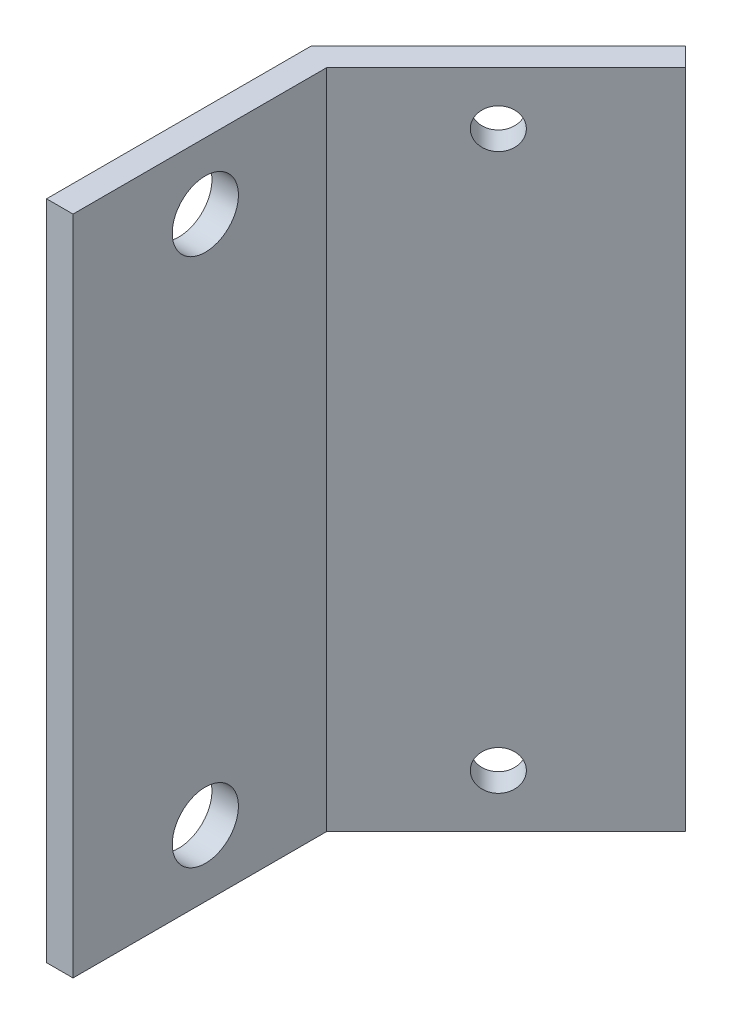
SolidWorks part; units mm, degrees
ref_plane "Plan de face" through (0, 0, 0) normal (0, 0, 1) x (1, 0, 0)
ref_plane "Plan de dessus" through (0, 0, 0) normal (0, 1, 0) x (1, 0, 0)
ref_plane "Plan de droite" through (0, 0, 0) normal (1, 0, 0) x (0, 0, -1)
sketch "Esquisse1" plane through (0, 0, 0) normal (0, 1, 0) x (1, 0, 0)
  line L0 (0, 0) -> (0, 20)
  line L1 (0, 20) -> (14.1421, 34.1421)
  line L2 (14.1421, 34.1421) -> (15.5563, 32.7279)
  line L3 (15.5563, 32.7279) -> (2, 19.1716)
  line L4 (2, 19.1716) -> (2, 0)
  line L5 (2, 0) -> (0, 0)
  dimension "D1" = 2
  dimension "D2" = 20
  dimension "D3" = 45
extrude "Extrusion1" add sketch "Esquisse1" along normal blind 50
sketch "Esquisse3" plane through (0, 0, 0) normal (-1, 0, 0) x (0, 0, 1)
  line L0 (-10, 0) -> (-10, 50) construction
  line L1 (-20, 0) -> (0, 0) construction
  line L2 (-20, 50) -> (0, 50) construction
  line L3 (0, 25) -> (-20, 25) construction
  line L4 (0, 50) -> (0, 0) construction
  line L5 (-20, 50) -> (-20, 0) construction
  line L6 (0, 5) -> (-20, 5) construction
  circle A0 centre (-10, 5) radius 2.5
  circle A1 centre (-10, 45) radius 2.5
  dimension "D1" = 5
  dimension "D2" = 5
extrude "Extrusion2" cut sketch "Esquisse3" against normal up to next
sketch "Esquisse4" plane through (-10, 0, -10) normal (-0.7071, 0, -0.7071) x (-0.7071, 0, 0.7071)
  line L0 (-24.1421, 50) -> (-24.1421, 0) construction
  line L1 (-34.1421, 50) -> (-14.1421, 50) construction
  line L2 (-34.1421, 0) -> (-14.1421, 0) construction
  line L3 (-34.1421, 25) -> (-14.1421, 25) construction
  line L4 (-34.1421, 50) -> (-34.1421, 0) construction
  line L5 (-14.1421, 50) -> (-14.1421, 0) construction
  line L6 (-34.1421, 46) -> (-14.1421, 46) construction
  circle A0 centre (-24.1421, 46) radius 1.5
  circle A1 centre (-24.1421, 4) radius 1.5
  dimension "D2" = 3
  dimension "D1" = 4
extrude "Extrusion3" cut sketch "Esquisse4" against normal up to next
